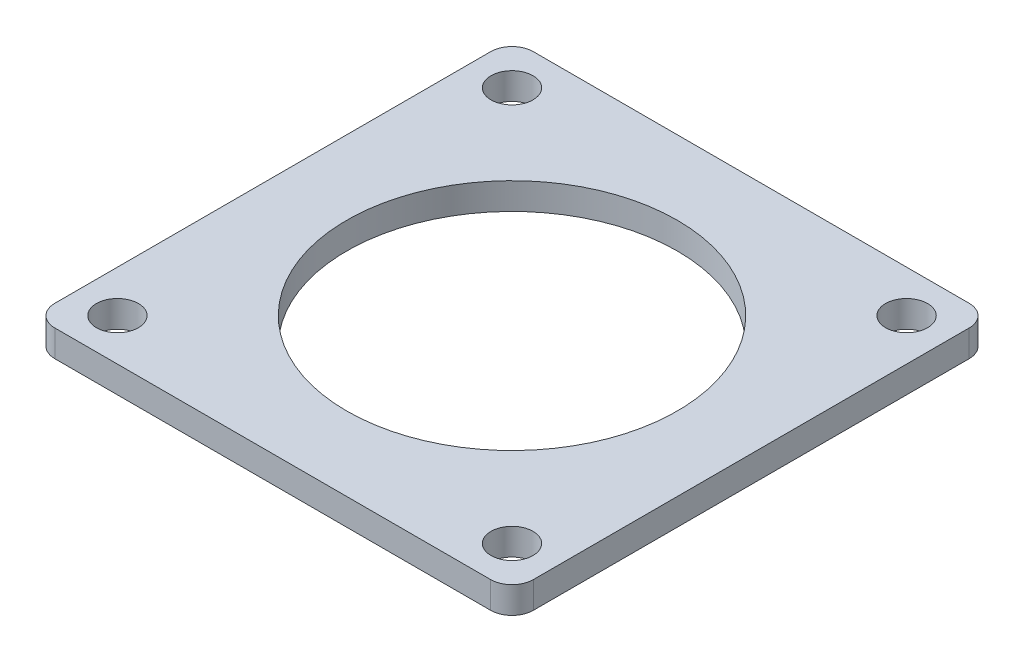
SolidWorks part; units mm, degrees
ref_plane "Front Plane" through (0, 0, 0) normal (0, 0, 1) x (1, 0, 0)
ref_plane "Top Plane" through (0, 0, 0) normal (0, 1, 0) x (1, 0, 0)
ref_plane "Right Plane" through (0, 0, 0) normal (1, 0, 0) x (0, 0, -1)
sketch "Sketch1" plane through (0, 0, 0) normal (0, 1, 0) x (1, 0, 0)
  line L0 (-13.9933, 28.5) -> (-25.96, 28.5)
  line L1 (25.96, -28.5) -> (13.9933, -28.5)
  line L2 (28.5, -25.96) -> (28.5, -13.9933)
  line L3 (25.96, 28.5) -> (13.9933, 28.5)
  line L4 (-28.5, -25.96) -> (-28.5, -13.9933)
  line L5 (28.5, -28.5) -> (-28.5, 28.5) construction
  line L6 (28.5, 28.5) -> (-28.5, -28.5) construction
  line L7 (28.5, 13.9933) -> (28.5, 25.96)
  line L8 (-13.9933, -28.5) -> (-25.96, -28.5)
  line L9 (-28.5, 13.9933) -> (-28.5, 25.96)
  line L10 (-28.5, 13.9933) -> (-28.5, -13.9933)
  line L11 (-13.9933, -28.5) -> (13.9933, -28.5)
  line L12 (-13.9933, 28.5) -> (13.9933, 28.5)
  line L13 (28.5, 13.9933) -> (28.5, -13.9933)
  circle A0 centre (0, 0) radius 19.685
  arc A5 (-25.96, -28.5) -> (-28.5, -25.96) centre (-25.96, -25.96) cw
  arc A6 (25.96, -28.5) -> (28.5, -25.96) centre (25.96, -25.96) ccw
  arc A7 (28.5, 25.96) -> (25.96, 28.5) centre (25.96, 25.96) ccw
  arc A8 (-25.96, 28.5) -> (-28.5, 25.96) centre (-25.96, 25.96) ccw
  circle A9 centre (-23.5, 23.5) radius 2.5
  circle A10 centre (23.5, 23.5) radius 2.5
  circle A11 centre (23.5, -23.5) radius 2.5
  circle A12 centre (-23.5, -23.5) radius 2.5
  point P38 (0, 0)
  dimension "D4" = 2.54
  dimension "D5" = 39.37
  dimension "D6" = 5
  dimension "D2" = 57
  dimension "D3" = 57
  dimension "D7" = 5
  dimension "D8" = 4
extrude "Boss-Extrude1" add sketch "Sketch1" along normal blind 3.175
